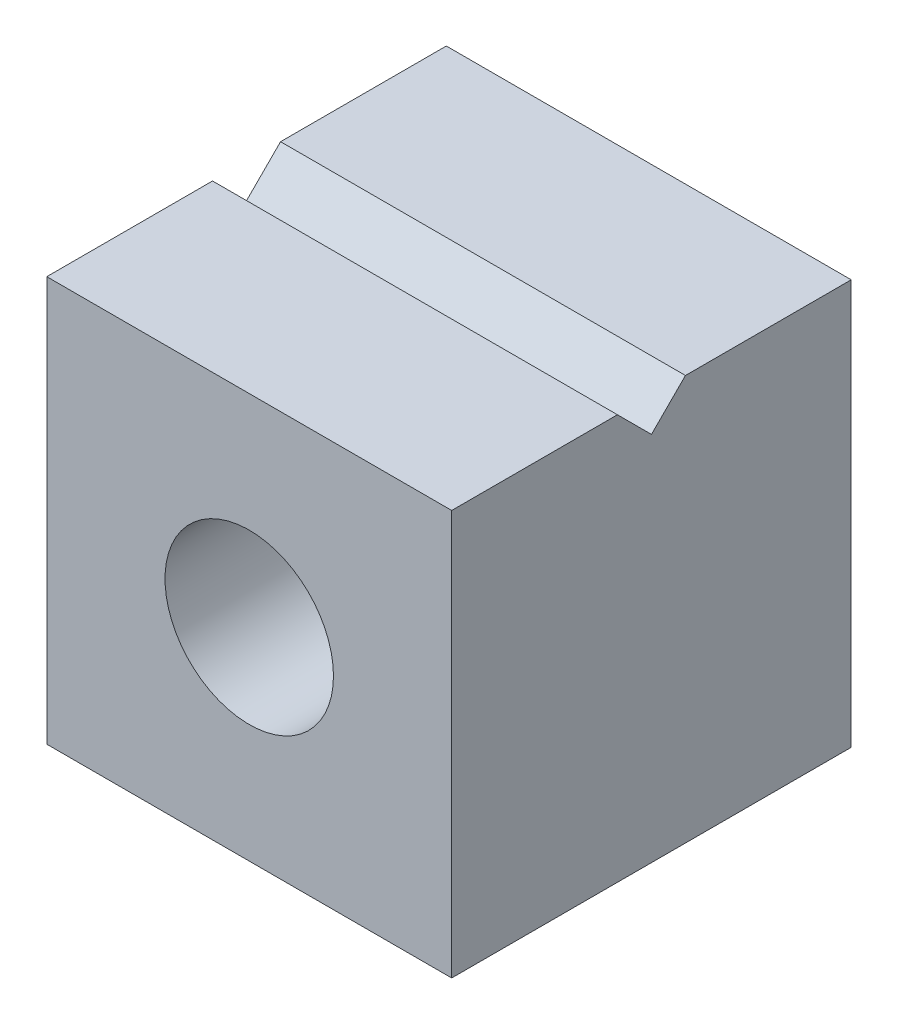
SolidWorks part; units mm, degrees
material "1023 Carbon Steel Sheet (SS)"
ref_plane "Front Plane" through (0, 0, 0) normal (0, 0, 1) x (1, 0, 0)
ref_plane "Top Plane" through (0, 0, 0) normal (0, 1, 0) x (1, 0, 0)
ref_plane "Right Plane" through (0, 0, 0) normal (1, 0, 0) x (0, 0, -1)
sketch "Sketch1" plane through (0, 0, 0) normal (0, 0, 1) x (1, 0, 0)
  line L1 (-3.75, -3.75) -> (3.75, -3.75)
  line L2 (-3.75, -3.75) -> (-3.75, 3.75)
  line L3 (-3.75, 3.75) -> (3.75, 3.75)
  line L4 (3.75, -3.75) -> (3.75, 3.75)
  line L5 (-3.75, -3.75) -> (3.75, 3.75) construction
  line L6 (-3.75, 3.75) -> (3.75, -3.75) construction
  circle A0 centre (0, 0) radius 1.56
  point P0 (0, 0)
  dimension "D2" = 3.12
  dimension "D1" = 7.5
extrude "Boss-Extrude1" add sketch "Sketch1" along normal blind 7.4
sketch "Sketch2" plane through (3.75, 0, 0) normal (1, 0, 0) x (0, 0, -1)
  line L0 (0, 0) -> (-7.4, 0) construction
  line L1 (-7.4, -3.75) -> (-7.4, 3.75) construction
  line L2 (-3.7, 0) -> (-3.7, 3.75) construction
  line L3 (-7.4, 3.75) -> (0, 3.75) construction
  line L4 (-3.7, 3.12) -> (-4.33, 3.75)
  line L5 (-4.33, 3.75) -> (-3.07, 3.75)
  line L6 (-3.7, 3.12) -> (-3.07, 3.75)
  dimension "D1" = 90
  dimension "D2" = 0.63
extrude "Cut-Extrude1" cut sketch "Sketch2" against normal through all
